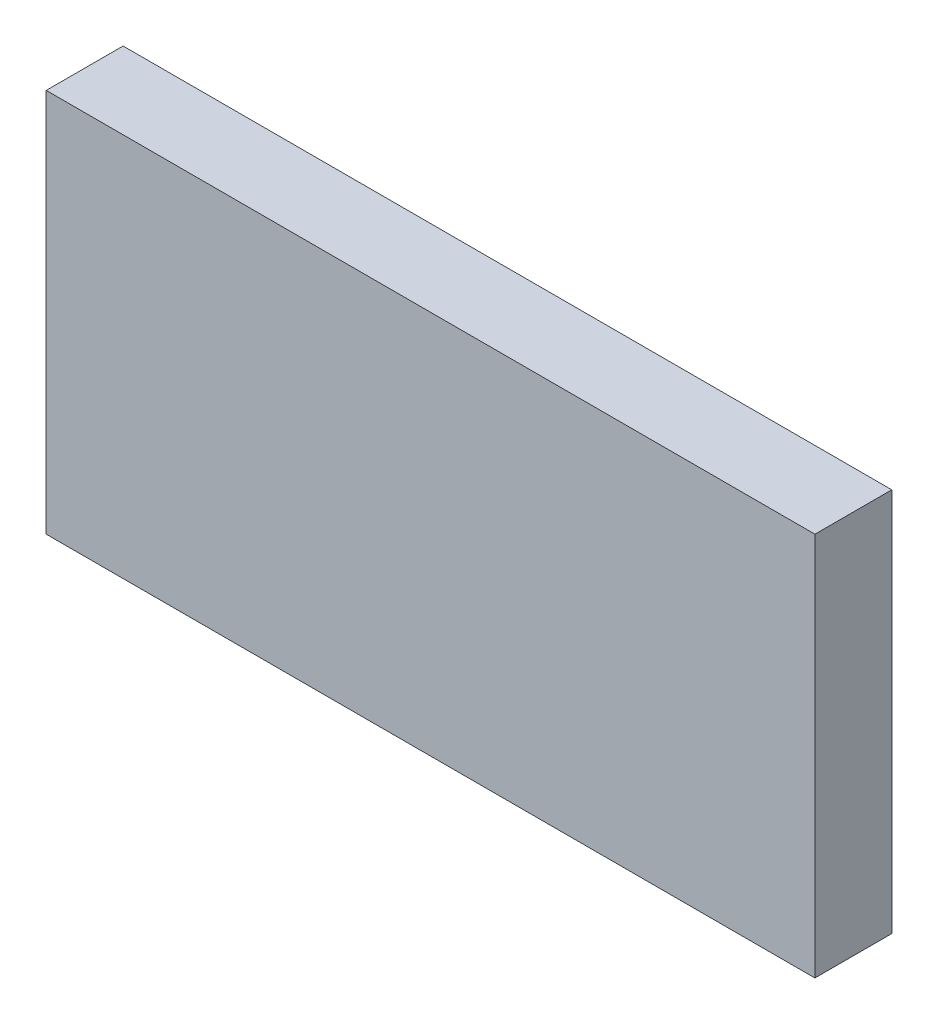
SolidWorks part; units mm, degrees
ref_plane "Plan de face" through (0, 0, 0) normal (0, 0, 1) x (1, 0, 0)
ref_plane "Plan de dessus" through (0, 0, 0) normal (0, 1, 0) x (1, 0, 0)
ref_plane "Plan de droite" through (0, 0, 0) normal (1, 0, 0) x (0, 0, -1)
sketch "Esquisse1" plane through (0, 0, 0) normal (0, 0, 1) x (1, 0, 0)
  line L1 (-50, -25) -> (50, -25)
  line L2 (-50, -25) -> (-50, 25)
  line L3 (-50, 25) -> (50, 25)
  line L4 (50, -25) -> (50, 25)
  line L5 (-50, -25) -> (50, 25) construction
  line L6 (-50, 25) -> (50, -25) construction
  point P0 (0, 0)
  dimension "D1" = 100
  dimension "D2" = 50
extrude "Boss.-Extru.1" add sketch "Esquisse1" along normal mid plane 10
